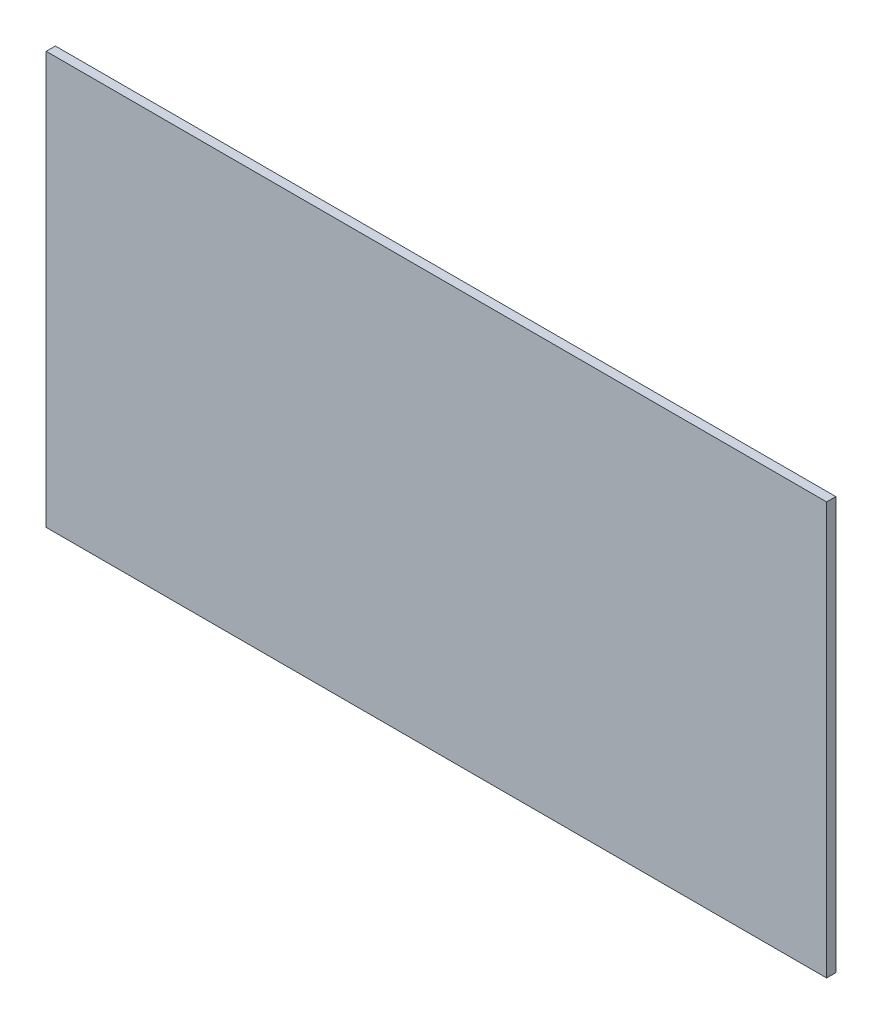
SolidWorks part; units mm, degrees
ref_plane "Front Plane" through (0, 0, 0) normal (0, 0, 1) x (1, 0, 0)
ref_plane "Top Plane" through (0, 0, 0) normal (0, 1, 0) x (1, 0, 0)
ref_plane "Right Plane" through (0, 0, 0) normal (1, 0, 0) x (0, 0, -1)
sketch "Sketch1" plane through (0, 0, 0) normal (0, 0, 1) x (1, 0, 0)
  line L0 (0, 0) -> (1700, 0)
  line L1 (1700, 0) -> (1700, 898.1572)
  line L2 (1700, 898.1572) -> (0, 898.1572)
  line L3 (0, 898.1572) -> (0, 0)
extrude "Boss-Extrude1" add sketch "Sketch1" along normal blind 20
